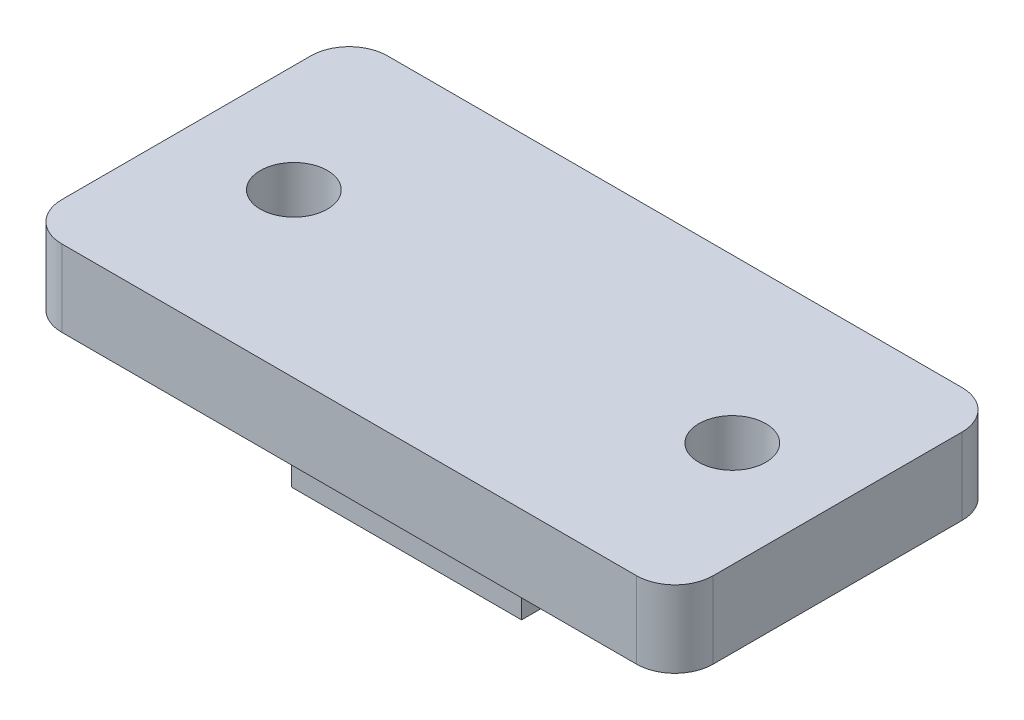
SolidWorks part; units mm, degrees
ref_plane "Front Plane" through (0, 0, 0) normal (0, 0, 1) x (1, 0, 0)
ref_plane "Top Plane" through (0, 0, 0) normal (0, 1, 0) x (1, 0, 0)
ref_plane "Right Plane" through (0, 0, 0) normal (1, 0, 0) x (0, 0, -1)
sketch "Sketch1" plane through (0, 0, 0) normal (0, 1, 0) x (1, 0, 0)
  line L1 (0, 0) -> (12, 0)
  line L2 (0, 0) -> (0, -11)
  line L3 (0, -11) -> (12, -11)
  line L4 (12, 0) -> (12, -11)
  dimension "D1" = 12
  dimension "D2" = 11
extrude "Boss-Extrude1" add sketch "Sketch1" along normal blind 4
sketch "Sketch2" plane through (0, 4, 0) normal (0, 1, 0) x (1, 0, 0)
  line L0 (0, 0) -> (12, -11) construction
  line L1 (12, 0) -> (0, 0) construction
  line L2 (-11, 3) -> (23, 3)
  line L3 (-11, 3) -> (-11, -14)
  line L4 (-11, -14) -> (23, -14)
  line L5 (23, 3) -> (23, -14)
  line L6 (-11, 3) -> (23, -14) construction
  line L7 (-11, -14) -> (23, 3) construction
  line L9 (0, 0) -> (0, -11) construction
  point P4 (6, -5.5)
  dimension "D1" = 3
  dimension "D2" = 11
extrude "Boss-Extrude2" add sketch "Sketch2" along normal blind 4
sketch "Sketch3" plane through (0, 4, 0) normal (0, -1, 0) x (1, 0, 0)
  line L0 (0, 5.5) -> (-11, 5.5) construction
  line L1 (0, 0) -> (0, 11) construction
  line L2 (-11, -3) -> (-11, 14) construction
  line L3 (12, 5.5) -> (23, 5.5) construction
  line L4 (12, 11) -> (12, 0) construction
  line L5 (23, 14) -> (23, -3) construction
  circle A0 centre (-5.3854, 5.5) radius 1.75
  circle A1 centre (17.5, 5.5) radius 1.75
  dimension "D1" = 3.5
extrude "Cut-Extrude1" cut sketch "Sketch3" against normal through all
fillet "Fillet1" radius 2 4 edges at (-11, 6, 14) (-11, 6, -3) (23, 6, -3) (23, 6, 14)
